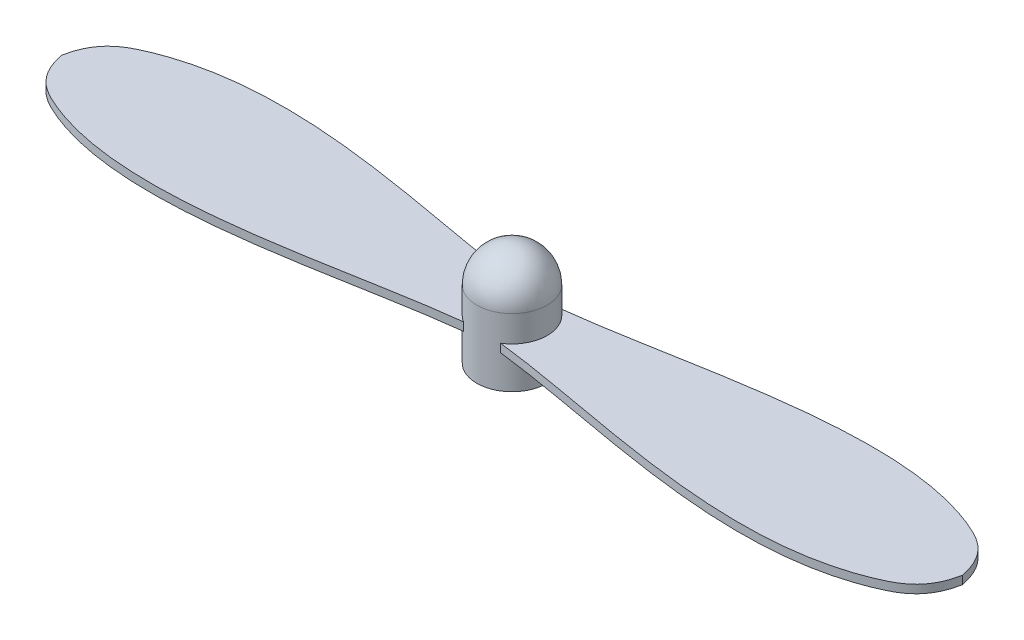
SolidWorks part; units mm, degrees
ref_plane "Front Plane" through (0, 0, 0) normal (0, 0, 1) x (1, 0, 0)
ref_plane "Top Plane" through (0, 0, 0) normal (0, 1, 0) x (1, 0, 0)
ref_plane "Right Plane" through (0, 0, 0) normal (1, 0, 0) x (0, 0, -1)
sketch "Sketch1" plane through (0, 0, 0) normal (0, 1, 0) x (1, 0, 0)
  circle A0 centre (0, 0) radius 2.13
  dimension "D1" = 4.26
extrude "Boss-Extrude1" add sketch "Sketch1" along normal blind 6.22
sketch "Sketch2" plane through (0, 0, 0) normal (0, -1, 0) x (1, 0, 0)
  circle A0 centre (0, 0) radius 0.5
  dimension "D1" = 1
extrude "Cut-Extrude1" cut sketch "Sketch2" against normal blind 5
fillet "Fillet1" radius 2.13 1 edges at (0, 6.22, 2.13)
ref_plane "Plane1" through (0, 2, 0) normal (0, -1, 0) x (-1, 0, 0)
sketch "Sketch3" plane through (0, 2, 0) normal (0, -1, 0) x (-1, 0, 0)
  line L0 (27.225, 0) -> (-27.225, 0) construction
  line L1 (0, 27.225) -> (0, -27.225) construction
  circle A0 centre (0, 0) radius 27.225
  circle A1 centre (0, 0) radius 2.13 construction
  circle A2 centre (0, 0) radius 2.13
  spline S0 degree 3 poles (27.225, 0) (26.8837, 1.7076) (19.5902, 6.2181) (7.7911, 2.5647) (1.1217, 1.8107) knots 0 0 0 0 0.130362 1 1 1 1
  spline S1 degree 3 poles (27.225, 0) (26.8837, -1.7076) (19.5902, -6.2181) (7.7911, -2.5647) (1.1217, -1.8107) knots 0 0 0 0 0.130362 1 1 1 1
  spline S2 degree 3 poles (-27.225, 0) (-26.8837, 1.7076) (-19.5902, 6.2181) (-7.7911, 2.5647) (-1.1217, 1.8107) knots 0 0 0 0 0.130362 1 1 1 1
  spline S3 degree 3 poles (-27.225, 0) (-26.8837, -1.7076) (-19.5902, -6.2181) (-7.7911, -2.5647) (-1.1217, -1.8107) knots 0 0 0 0 0.130362 1 1 1 1
  dimension "D1" = 54.45
extrude "Boss-Extrude2" add sketch "Sketch3" against normal blind 0.5 contours S1 S0 A2 | S2 S3 A2
